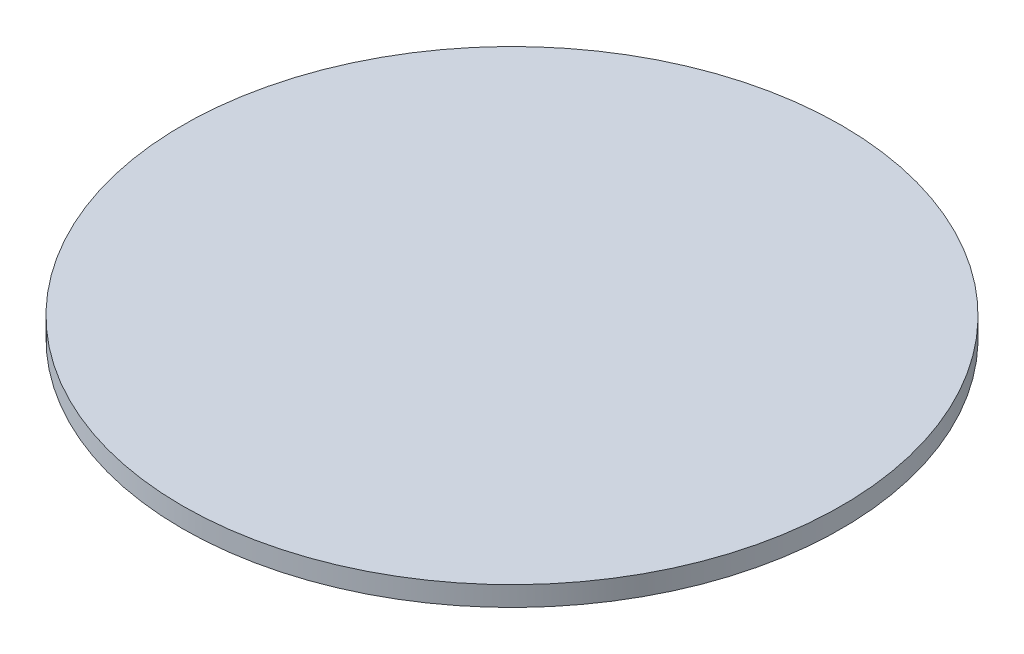
SolidWorks part; units mm, degrees
ref_plane "Front Plane" through (0, 0, 0) normal (0, 0, 1) x (1, 0, 0)
ref_plane "Top Plane" through (0, 0, 0) normal (0, 1, 0) x (1, 0, 0)
ref_plane "Right Plane" through (0, 0, 0) normal (1, 0, 0) x (0, 0, -1)
sketch "Sketch1" plane through (0, 0, 0) normal (0, 1, 0) x (1, 0, 0)
  circle A0 centre (0, 0) radius 12.7
  dimension "D1" = 25.4
extrude "Boss-Extrude1" add sketch "Sketch1" along normal blind 0.762
